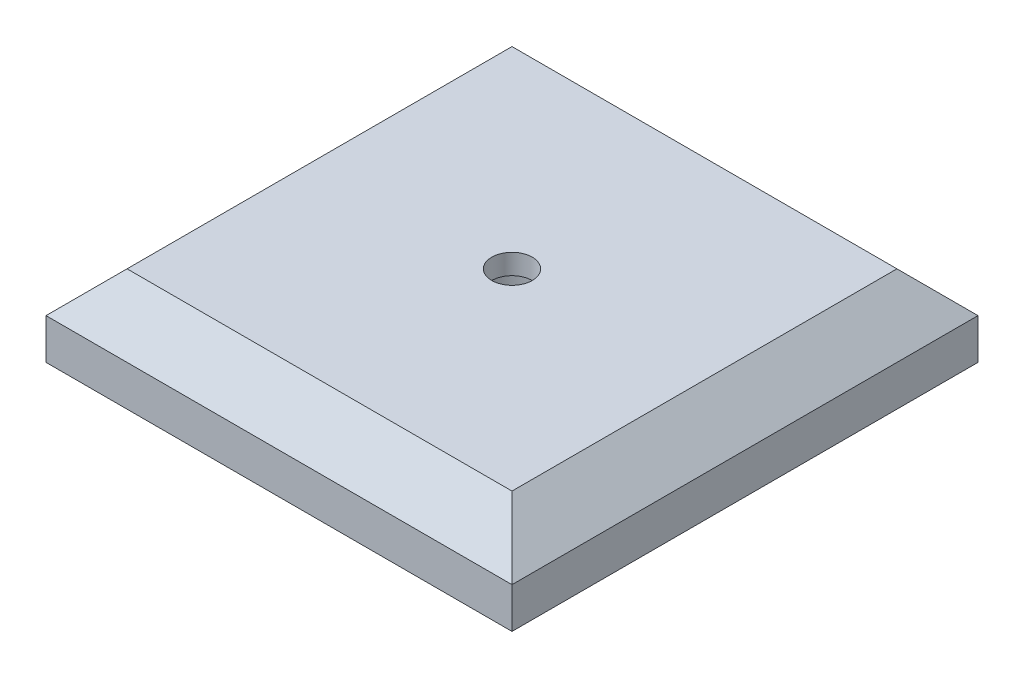
SolidWorks part; units mm, degrees
ref_plane "Front Plane" through (0, 0, 0) normal (0, 0, 1) x (1, 0, 0)
ref_plane "Top Plane" through (0, 0, 0) normal (0, 1, 0) x (1, 0, 0)
ref_plane "Right Plane" through (0, 0, 0) normal (1, 0, 0) x (0, 0, -1)
sketch "Sketch1" plane through (0, 0, 0) normal (0, 1, 0) x (1, 0, 0)
  line L1 (-14.375, 14.375) -> (14.375, 14.375)
  line L2 (-14.375, 14.375) -> (-14.375, -14.375)
  line L3 (-14.375, -14.375) -> (14.375, -14.375)
  line L4 (14.375, 14.375) -> (14.375, -14.375)
  line L5 (-14.375, 14.375) -> (14.375, -14.375) construction
  line L6 (-14.375, -14.375) -> (14.375, 14.375) construction
  point P0 (0, 0)
  dimension "D1" = 28.75
  dimension "D2" = 28.75
extrude "Boss-Extrude4" add sketch "Sketch1" along normal blind 2.5
sketch "Sketch5" plane through (0, 2.5, 0) normal (0, 1, 0) x (1, 0, 0)
  line L1 (-14.375, 14.375) -> (14.375, 14.375)
  line L2 (-14.375, 14.375) -> (-14.375, -14.375)
  line L3 (-14.375, -14.375) -> (14.375, -14.375)
  line L4 (14.375, 14.375) -> (14.375, -14.375)
  line L5 (-14.375, 14.375) -> (14.375, -14.375) construction
  line L6 (-14.375, -14.375) -> (14.375, 14.375) construction
  point P0 (0, 0)
extrude "Boss-Extrude5" add sketch "Sketch5" along normal blind 2.5 draft 45
sketch "Sketch6" plane through (0, 5, 0) normal (0, 1, 0) x (1, 0, 0)
  circle A0 centre (0, 0) radius 1.25
  dimension "D1" = 2.5
extrude "Cut-Extrude5" cut sketch "Sketch6" against normal blind 1.25
sketch "Sketch10" plane through (0, 0, 0) normal (0, -1, 0) x (1, 0, 0)
  circle A0 centre (0, 0) radius 2.5
  dimension "D1" = 5
extrude "Cut-Extrude6" cut sketch "Sketch10" against normal blind 3.75
